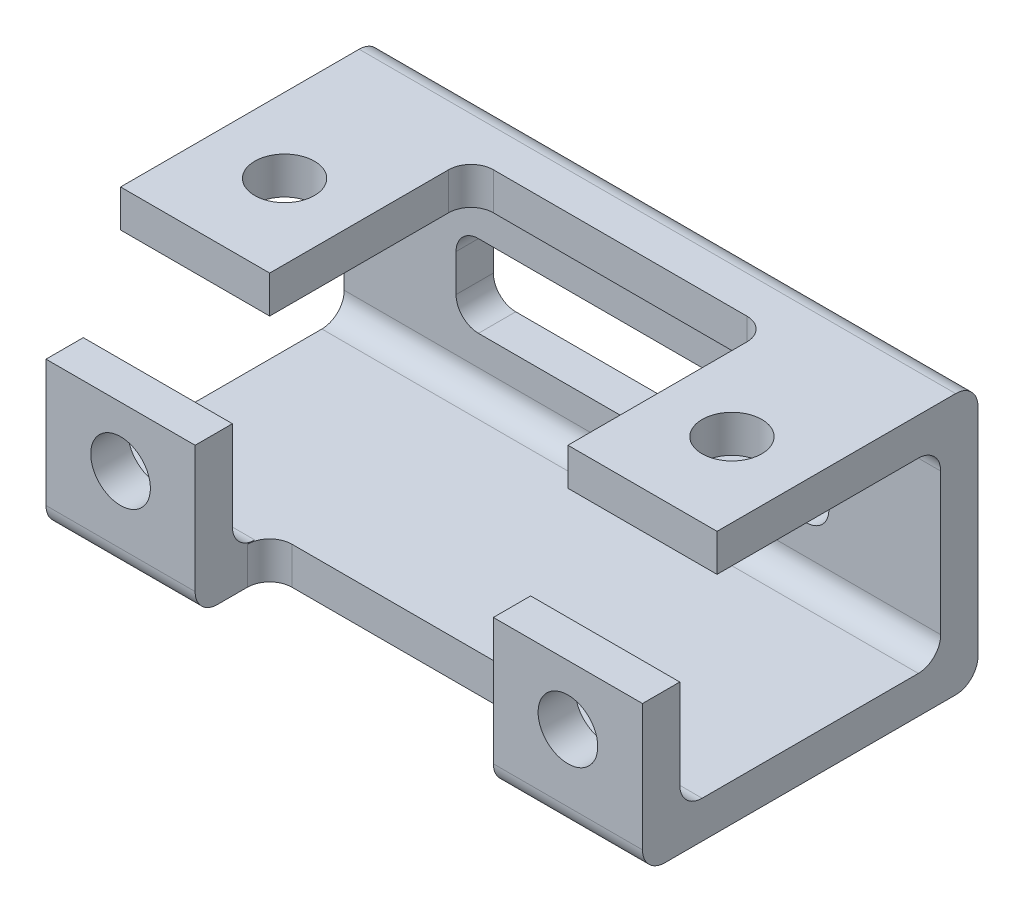
SolidWorks part; units mm, degrees
material "Nickel"
ref_plane "Front Plane" through (0, 0, 0) normal (0, 0, 1) x (1, 0, 0)
ref_plane "Top Plane" through (0, 0, 0) normal (0, 1, 0) x (1, 0, 0)
ref_plane "Right Plane" through (0, 0, 0) normal (1, 0, 0) x (0, 0, -1)
sketch "Sketch1" plane through (0, 0, 0) normal (0, 0, 1) x (1, 0, 0)
  line L1 (40, 17.5) -> (-40, 17.5)
  line L2 (40, 17.5) -> (40, -17.5)
  line L3 (40, -17.5) -> (-40, -17.5)
  line L4 (-40, 17.5) -> (-40, -17.5)
  line L5 (40, 17.5) -> (-40, -17.5) construction
  line L6 (40, -17.5) -> (-40, 17.5) construction
  point P0 (0, 0)
  dimension "D1" = 80
  dimension "D2" = 35
extrude "Rectangle Block Extrude" add sketch "Sketch1" along normal blind 45 contours L2 L3 L4 L1
sketch "Sketch11" plane through (-40, 0, 0) normal (-1, 0, 0) x (0, 0, 1)
  line L0 (22.5, 17.5) -> (22.5, -17.5) construction
  line L1 (45, 17.5) -> (0, 17.5) construction
  line L2 (45, -17.5) -> (0, -17.5) construction
  line L3 (0, 0) -> (45, 0) construction
  line L4 (45, 17.5) -> (45, -17.5) construction
  line L5 (0, 17.5) -> (0, -17.5) construction
  line L6 (8, 12.5) -> (37, 12.5)
  line L7 (5, 9.5) -> (5, -9.5)
  line L8 (8, -12.5) -> (37, -12.5)
  line L9 (40, 9.5) -> (40, -9.5)
  line L10 (5, 12.5) -> (40, -12.5) construction
  line L11 (5, -12.5) -> (40, 12.5) construction
  arc A0 (37, 12.5) -> (40, 9.5) centre (37, 9.5) cw
  arc A1 (37, -12.5) -> (40, -9.5) centre (37, -9.5) ccw
  arc A2 (5, -9.5) -> (8, -12.5) centre (8, -9.5) ccw
  arc A3 (8, 12.5) -> (5, 9.5) centre (8, 9.5) ccw
  point P13 (22.5, 0)
  dimension "D3" = 3
  dimension "D1" = 5
  dimension "D2" = 5
extrude "Hollow Out Block Cut" cut sketch "Sketch11" against normal through all
sketch "Sketch12" plane through (-40, 0, 0) normal (-1, 0, 0) x (0, 0, 1)
  line L2 (35, 17.5) -> (35, 12.5)
  line L3 (45, 17.5) -> (0, 17.5) construction
  line L4 (37, 12.5) -> (8, 12.5) construction
  line L5 (40, 2.5) -> (45, 2.5)
  line L6 (40, -9.5) -> (40, 9.5) construction
  line L7 (45, 17.5) -> (45, -17.5) construction
  line L8 (37, 12.5) -> (35, 12.5)
  line L9 (40, 2.5) -> (40, 9.5)
  line L12 (0, 17.5) -> (0, -17.5)
  line L13 (0, -17.5) -> (45, -17.5)
  line L14 (45, -17.5) -> (45, 17.5)
  line L15 (45, 17.5) -> (0, 17.5)
  line L18 (45, 2.5) -> (45, 17.5)
  line L19 (45, 17.5) -> (35, 17.5)
  arc A0 (40, 9.5) -> (37, 12.5) centre (37, 9.5) ccw construction
  arc A1 (40, 9.5) -> (37, 12.5) centre (37, 9.5) ccw
  dimension "D1" = 0
  dimension "D2" = 35
  dimension "D3" = 20
extrude "Open Corner Cut" cut sketch "Sketch12" against normal through all
ref_plane "Plane5" through (0, 17.5, 0) normal (0, 1, 0) x (1, 0, 0)
sketch "Sketch15" plane through (0, 17.5, 0) normal (0, 1, 0) x (1, 0, 0)
  line L0 (0, 22.038) -> (0, -59.9796) construction
  line L1 (-17, -8) -> (17, -8)
  line L2 (-20, -11) -> (-20, -35)
  line L3 (-20, -35) -> (20, -35)
  line L4 (-40, 0) -> (-40, -35)
  line L5 (-40, -35) -> (40, -35)
  line L6 (40, -35) -> (40, 0)
  line L7 (40, 0) -> (-40, 0)
  line L9 (-20, -35) -> (40, -35)
  line L12 (20, -11) -> (20, -35)
  arc A0 (17, -8) -> (20, -11) centre (17, -11) cw
  arc A1 (-17, -8) -> (-20, -11) centre (-17, -11) ccw
  circle A2 centre (-30, -23) radius 4
  circle A3 centre (30, -23) radius 4
  dimension "D5" = 3
  dimension "D6" = 8
  dimension "D7" = 12
  dimension "D3" = 20
  dimension "D4" = 20
  dimension "D1" = 0
extrude "Top Cuts" cut sketch "Sketch15" against normal up to next contours A2 | L0 L1 A1 L2 L3 | L1 L0 L9 L12 A0 | A3
ref_plane "Plane6" through (0, 0, 35) normal (0, 0, 1) x (1, 0, 0)
sketch "Sketch18" plane through (0, 0, 35) normal (0, 0, 1) x (1, 0, 0)
  line L4 (40, 2.5) -> (-40, 2.5)
  line L5 (-40, 2.5) -> (-40, -17.5)
  line L6 (-40, -17.5) -> (40, -17.5)
  line L7 (40, -17.5) -> (40, 2.5)
  line L9 (-40, 2.5) -> (-40, -17.5)
  circle A2 centre (-30, -5.5) radius 4
  circle A3 centre (30, -5.5) radius 4
  point P2 (0, 0)
  dimension "D5" = 8
  dimension "D6" = 10
  dimension "D1" = 0
extrude "Circle Cut on Front" cut sketch "Sketch18" along normal up to next contours A2 | A3
sketch "Sketch23" plane through (0, 0, 0) normal (0, 0, -1) x (-1, 0, 0)
  line L1 (22, 5.5) -> (-22, 5.5)
  line L2 (25, 2.5) -> (25, -2.5)
  line L3 (22, -5.5) -> (-22, -5.5)
  line L12 (-25, 2.5) -> (-25, -2.5)
  line L13 (25, 5.5) -> (-25, -5.5) construction
  line L14 (25, -5.5) -> (-25, 5.5) construction
  arc A0 (22, 5.5) -> (25, 2.5) centre (22, 2.5) cw
  arc A1 (25, -2.5) -> (22, -5.5) centre (22, -2.5) cw
  arc A2 (-22, -5.5) -> (-25, -2.5) centre (-22, -2.5) cw
  arc A3 (-22, 5.5) -> (-25, 2.5) centre (-22, 2.5) ccw
  point P2 (0, 0)
  dimension "D4" = 3
extrude "Rectangle Cut on Back" cut sketch "Sketch23" against normal blind 5 contours A3 L12 A2 L3 A1 L2 A0 L1
sketch "Sketch24" plane through (-40, 0, 0) normal (-1, 0, 0) x (0, 0, 1)
  line L0 (3, -17.5) -> (0, -17.5)
  line L1 (0, -17.5) -> (0, -14.5)
  line L2 (0, 14.5) -> (0, 17.5)
  line L5 (17.6, 17.5) -> (-17.6, 17.5) construction
  line L6 (42, -17.5) -> (45, -17.5)
  line L7 (45, -17.5) -> (45, -14.5)
  line L8 (0, 17.5) -> (0, -17.5) construction
  line L9 (0, 17.5) -> (3, 17.5)
  arc A0 (45, -14.5) -> (42, -17.5) centre (42, -14.5) cw
  arc A1 (0, -14.5) -> (3, -17.5) centre (3, -14.5) ccw
  arc A2 (3, 17.5) -> (0, 14.5) centre (3, 14.5) ccw
  dimension "D2" = 3
extrude "Cut-Extrude17" cut sketch "Sketch24" against normal through all
sketch "Sketch25" plane through (0, 0, 45) normal (0, 0, 1) x (1, 0, 0)
  line L1 (-40, -17.5) -> (40, -17.5) construction
  line L5 (40, 2.5) -> (-40, 2.5) construction
  line L7 (-20, -17.5) -> (20, -17.5)
  line L11 (20, 2.5) -> (-20, 2.5)
  line L13 (20, 27.5617) -> (-20, 27.5617)
  line L14 (20, 2.5) -> (20, -17.5)
  line L16 (-20, 2.5) -> (-20, -17.5)
  line L17 (1.8141, 2.5) -> (-12.6988, -17.5) construction
  line L18 (12.6988, -17.5) -> (-1.8141, 2.5) construction
  point P2 (0, 0)
  dimension "D1" = 40
extrude "Cut-Extrude18" cut sketch "Sketch25" against normal blind 10
ref_plane "Plane7" through (0, -17.5, 0) normal (0, -1, 0) x (-1, 0, 0)
sketch "Sketch28" plane through (0, -17.5, 0) normal (0, -1, 0) x (-1, 0, 0)
  line L0 (-20, -38) -> (-20, -35)
  line L1 (-20, -35) -> (-20, -42) construction
  line L2 (-20, -35) -> (-17, -35)
  line L3 (20, -38) -> (20, -35)
  line L4 (20, -35) -> (17, -35)
  arc A0 (17, -35) -> (20, -38) centre (17, -38) cw
  arc A1 (-20, -38) -> (-17, -35) centre (-17, -38) cw
  dimension "D2" = 3
extrude "Boss-Extrude6" add sketch "Sketch28" against normal blind 5
equation "\"Hole Diameter\"= 8"
